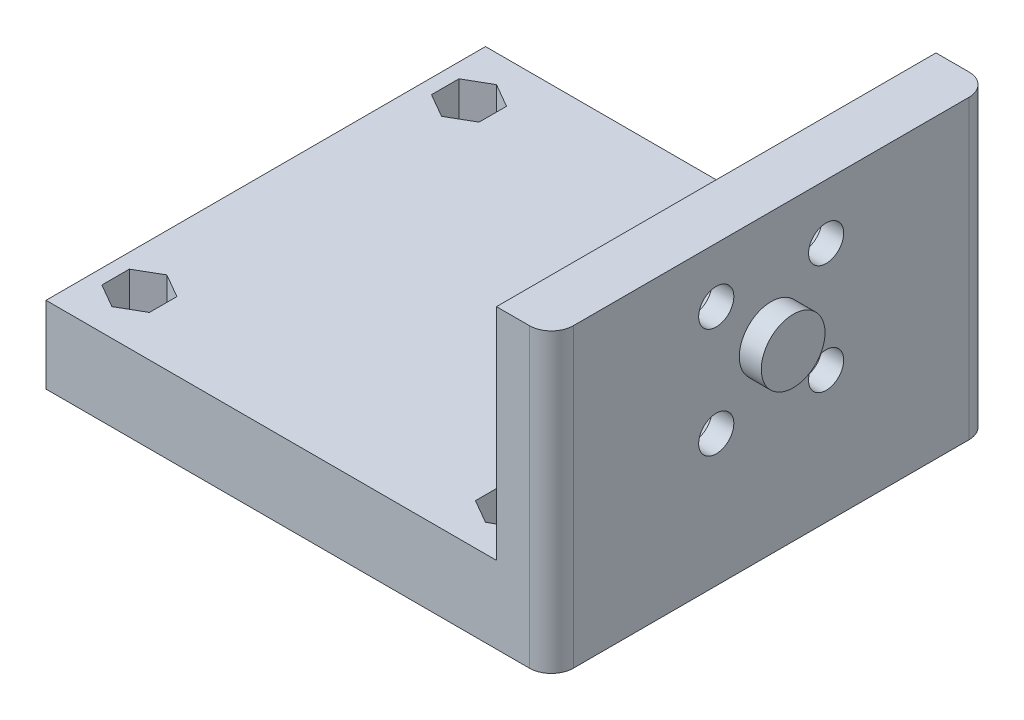
SolidWorks part; units mm, degrees
ref_plane "Plan de face" through (0, 0, 0) normal (0, 0, 1) x (1, 0, 0)
ref_plane "Plan de dessus" through (0, 0, 0) normal (0, 1, 0) x (1, 0, 0)
ref_plane "Plan de droite" through (0, 0, 0) normal (1, 0, 0) x (0, 0, -1)
sketch "Esquisse1" plane through (0, 0, 0) normal (0, 1, 0) x (1, 0, 0)
  line L1 (0, 20) -> (-5, 20)
  line L2 (0, 20) -> (0, -20)
  line L3 (0, -20) -> (-5, -20)
  line L4 (-5, 20) -> (-5, -20)
  dimension "D1" = 5
  dimension "D2" = 40
  dimension "D3" = 20
extrude "Boss.-Extru.1" add sketch "Esquisse1" against normal blind 27
sketch "Esquisse2" plane through (-5, 0, 0) normal (-1, 0, 0) x (0, 0, 1)
  line L0 (-20, -27) -> (-20, 0) construction
  line L1 (20, -27) -> (-20, -27)
  line L2 (20, -27) -> (20, -20)
  line L3 (20, -20) -> (-20, -20)
  line L4 (-20, -27) -> (-20, -20)
  dimension "D1" = 7
extrude "Boss.-Extru.2" add sketch "Esquisse2" along normal blind 41
fillet "Congé1" radius 2 2 edges at (0, -13.5, -20) (0, -13.5, 20)
sketch "Esquisse4" plane through (0, 0, 0) normal (1, 0, 0) x (0, 0, -1)
  circle A0 centre (-5, -5) radius 1.6
  circle A1 centre (5, -5) radius 1.6
  circle A2 centre (-5, -15) radius 1.6
  circle A3 centre (5, -15) radius 1.6
  dimension "D1" = 10
  dimension "D3" = 3.2
  dimension "D2" = 10
  dimension "D4" = 5
  dimension "D5" = 5
extrude "Enlèv. mat.-Extru.1" cut sketch "Esquisse4" against normal up to next
sketch "Esquisse5" plane through (0, 0, 0) normal (1, 0, 0) x (0, 0, -1)
  line L1 (-18, 0) -> (18, 0) construction
  line L4 (20, 0) -> (20, -27) construction
  circle A0 centre (0, -10) radius 2.9
  dimension "D1" = 5.8
  dimension "D2" = 10
  dimension "D4" = 20
extrude "Boss.-Extru.3" add sketch "Esquisse5" along normal blind 2
sketch "Esquisse7" plane through (-5, 0, 0) normal (-1, 0, 0) x (0, 0, 1)
  line L1 (-3.25, -8.0311) -> (-1.5, -5)
  line L2 (-1.5, -5) -> (-3.25, -1.9689)
  line L3 (-3.25, -1.9689) -> (-6.75, -1.9689)
  line L4 (-6.75, -1.9689) -> (-8.5, -5)
  line L5 (-8.5, -5) -> (-6.75, -8.0311)
  line L6 (-6.75, -8.0311) -> (-3.25, -8.0311)
  line L7 (3.25, -1.9689) -> (1.5, -5)
  line L8 (1.5, -5) -> (3.25, -8.0311)
  line L9 (3.25, -8.0311) -> (6.75, -8.0311)
  line L10 (6.75, -8.0311) -> (8.5, -5)
  line L11 (8.5, -5) -> (6.75, -1.9689)
  line L12 (6.75, -1.9689) -> (3.25, -1.9689)
  line L13 (-3.25, -18.0311) -> (-1.5, -15)
  line L14 (-1.5, -15) -> (-3.25, -11.9689)
  line L15 (-3.25, -11.9689) -> (-6.75, -11.9689)
  line L16 (-6.75, -11.9689) -> (-8.5, -15)
  line L17 (-8.5, -15) -> (-6.75, -18.0311)
  line L18 (-6.75, -18.0311) -> (-3.25, -18.0311)
  line L19 (8.5, -15) -> (6.75, -11.9689)
  line L20 (6.75, -11.9689) -> (3.25, -11.9689)
  line L21 (3.25, -11.9689) -> (1.5, -15)
  line L22 (1.5, -15) -> (3.25, -18.0311)
  line L23 (3.25, -18.0311) -> (6.75, -18.0311)
  line L24 (6.75, -18.0311) -> (8.5, -15)
  line L25 (18, 0) -> (-18, 0) construction
  line L26 (-20, 0) -> (20, 0) construction
  circle A0 centre (-5, -5) radius 3.0311 construction
  circle A1 centre (5, -5) radius 3.0311 construction
  circle A2 centre (-5, -15) radius 3.0311 construction
  circle A3 centre (5, -15) radius 3.0311 construction
  circle A4 centre (5, -15) radius 1.6 construction
  dimension "D1" = 3.5
  dimension "D2" = 3.5
  dimension "D3" = 3.5
  dimension "D4" = 3.5
extrude "Enlèv. mat.-Extru.3" cut sketch "Esquisse7" against normal blind 3
sketch "Esquisse9" plane through (0, -20, 0) normal (0, 1, 0) x (1, 0, 0)
  line L0 (-5, -20) -> (-5, 20) construction
  line L1 (-46, -20) -> (-46, 20) construction
  line L4 (-46, -20) -> (-46, 20) construction
  circle A0 centre (-8.5, 15) radius 1.1
  circle A1 centre (-8.5, -15) radius 1.1
  circle A2 centre (-42.5, -15) radius 1.1
  circle A3 centre (-42.5, 15) radius 1.1
  point P8 (-46, 0)
  dimension "D1" = 2.2
  dimension "D5" = 15
  dimension "D2" = 3.5
  dimension "D3" = 3.5
  dimension "D4" = 30
extrude "Enlèv. mat.-Extru.5" cut sketch "Esquisse9" against normal through all
sketch "Esquisse8" plane through (0, -20, 0) normal (0, 1, 0) x (1, 0, 0)
  line L0 (-5, -20) -> (-5, 20) construction
  line L1 (-10.6651, 13.75) -> (-8.5, 12.5)
  line L2 (-8.5, 12.5) -> (-6.3349, 13.75)
  line L3 (-6.3349, 13.75) -> (-6.3349, 16.25)
  line L4 (-6.3349, 16.25) -> (-8.5, 17.5)
  line L5 (-8.5, 17.5) -> (-10.6651, 16.25)
  line L6 (-10.6651, 16.25) -> (-10.6651, 13.75)
  line L7 (-10.6651, -16.25) -> (-8.5, -17.5)
  line L8 (-8.5, -17.5) -> (-6.3349, -16.25)
  line L9 (-6.3349, -16.25) -> (-6.3349, -13.75)
  line L10 (-6.3349, -13.75) -> (-8.5, -12.5)
  line L11 (-8.5, -12.5) -> (-10.6651, -13.75)
  line L12 (-10.6651, -13.75) -> (-10.6651, -16.25)
  line L13 (-44.6651, -16.25) -> (-42.5, -17.5)
  line L14 (-42.5, -17.5) -> (-40.3349, -16.25)
  line L15 (-40.3349, -16.25) -> (-40.3349, -13.75)
  line L16 (-40.3349, -13.75) -> (-42.5, -12.5)
  line L17 (-42.5, -12.5) -> (-44.6651, -13.75)
  line L18 (-44.6651, -13.75) -> (-44.6651, -16.25)
  line L19 (-42.5, 12.5) -> (-40.3349, 13.75)
  line L20 (-40.3349, 13.75) -> (-40.3349, 16.25)
  line L21 (-40.3349, 16.25) -> (-42.5, 17.5)
  line L22 (-42.5, 17.5) -> (-44.6651, 16.25)
  line L23 (-44.6651, 16.25) -> (-44.6651, 13.75)
  line L24 (-44.6651, 13.75) -> (-42.5, 12.5)
  circle A0 centre (-8.5, 15) radius 2.1651 construction
  circle A1 centre (-8.5, -15) radius 2.1651 construction
  circle A2 centre (-42.5, -15) radius 2.1651 construction
  circle A3 centre (-42.5, 15) radius 2.1651 construction
  circle A4 centre (-8.5, 15) radius 1.1 construction
  circle A5 centre (-8.5, -15) radius 1.1 construction
  circle A7 centre (-42.5, 15) radius 1.1 construction
  dimension "D1" = 2.5
  dimension "D2" = 2.5
  dimension "D3" = 2.5
  dimension "D4" = 2.5
extrude "Enlèv. mat.-Extru.4" cut sketch "Esquisse8" against normal blind 4
